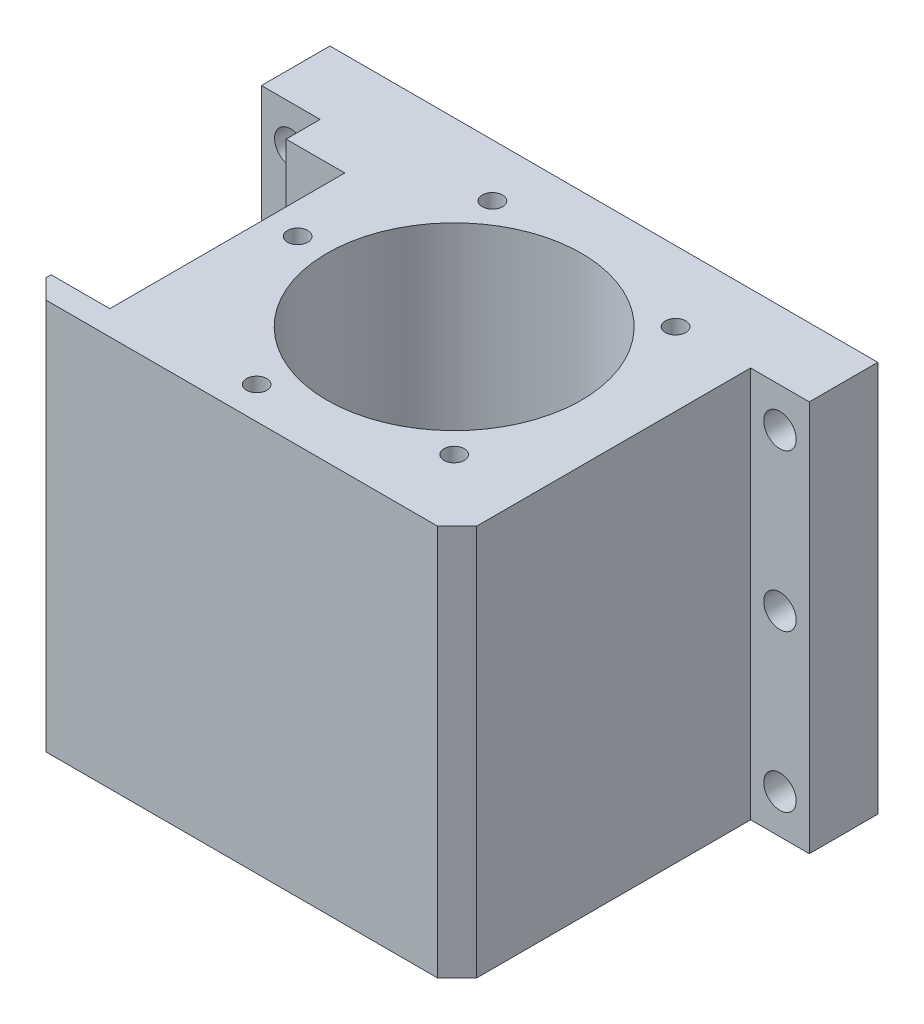
SolidWorks part; units mm, degrees
material "3.3315 (EN-AW 5005)"
ref_plane "前视基准面" through (0, 0, 0) normal (0, 0, 1) x (1, 0, 0)
ref_plane "上视基准面" through (0, 0, 0) normal (0, 1, 0) x (1, 0, 0)
ref_plane "右视基准面" through (0, 0, 0) normal (1, 0, 0) x (0, 0, -1)
other "Configuration Table"
sketch "草图1" plane through (0, 0, 0) normal (0, 0, 1) x (1, 0, 0)
  line L1 (0, 0) -> (140, 0)
  line L2 (0, 0) -> (0, -100)
  line L3 (0, -100) -> (140, -100)
  line L4 (140, 0) -> (140, -100)
  dimension "D1" = 140
  dimension "D2" = 100
extrude "凸台-拉伸1" add sketch "草图1" along normal blind 92.5
sketch "草图2" plane through (0, 0, 0) normal (0, 1, 0) x (1, 0, 0)
  line L0 (140, -46.25) -> (0, -46.25) construction
  line L1 (140, -92.5) -> (140, 0) construction
  line L2 (0, -92.5) -> (0, 0) construction
  circle A0 centre (78, -46.25) radius 32.525
  dimension "D1" = 65.05
  dimension "D2" = 62
extrude "切除-拉伸1" cut sketch "草图2" against normal through all
sketch "草图3" plane through (0, 0, 92.5) normal (0, 0, 1) x (1, 0, 0)
  line L0 (70, 0) -> (70, -100) construction
  line L1 (140, 0) -> (0, 0) construction
  line L2 (0, -100) -> (140, -100) construction
  line L3 (0, 0) -> (0, -100) construction
  line L4 (15, 0) -> (125, 0)
  line L5 (15, 0) -> (15, -100)
  line L6 (15, -100) -> (125, -100)
  line L7 (125, 0) -> (125, -100)
  dimension "D1" = 110
  dimension "D2" = 15
extrude "切除-拉伸2" cut sketch "草图3" against normal blind 75 flip side to cut
sketch "草图4" plane through (0, 0, 0) normal (0, 1, 0) x (1, 0, 0)
  circle A0 centre (78, -46.25) radius 46 construction
  dimension "D1" = 92
sketch "草图5" plane through (15, 0, 0) normal (-1, 0, 0) x (0, 0, 1)
  line L0 (46.25, 0) -> (46.25, -100) construction
  line L1 (92.25, 0) -> (0.25, 0) construction
  line L2 (17.5, -100) -> (92.5, -100) construction
  line L4 (26.2, 0) -> (86.25, 0)
  line L5 (26.2, 0) -> (26.2, -100)
  line L6 (26.2, -100) -> (86.25, -100)
  line L7 (86.25, 0) -> (86.25, -100)
  dimension "D1" = 60.05
  dimension "D2" = 40
extrude "切除-拉伸3" cut sketch "草图5" against normal blind 15
chamfer "倒角2" distance 5 angle 45 2 edges at (125, -50, 92.5) (15, -50, 92.5)
sketch "草图6" plane through (0, -100, 0) normal (0, -1, 0) x (1, 0, 0)
  line L0 (78, 46.25) -> (78, 92.25) construction
  circle A0 centre (78, 46.25) radius 39.5 construction
  circle A1 centre (78, 46.25) radius 46 construction
  circle A2 centre (78, 85.75) radius 2.6
  circle A3 centre (112.208, 66) radius 2.6
  circle A4 centre (112.208, 26.5) radius 2.6
  circle A5 centre (78, 6.75) radius 2.6
  circle A6 centre (43.792, 26.5) radius 2.6
  circle A7 centre (43.792, 66) radius 2.6
  point P20 (78, 46.25)
  dimension "D1" = 79
  dimension "D2" = 5.2
  dimension "D3" = 6
extrude "切除-拉伸4" cut sketch "草图6" against normal blind 20
sketch "草图9" plane through (0, 0, 17.5) normal (0, 0, 1) x (1, 0, 0)
  line L0 (0, 0) -> (0, -100) construction
  line L1 (15, 0) -> (0, 0) construction
  circle A0 centre (7.5, -10) radius 4.15
  circle A1 centre (132.5, -10) radius 4.15
  circle A2 centre (132.5, -50) radius 4.15
  circle A3 centre (132.5, -90) radius 4.15
  circle A4 centre (7.5, -50) radius 4.15
  circle A5 centre (7.5, -90) radius 4.15
  dimension "D1" = 8.3
  dimension "D4" = 2
  dimension "D2" = 7.5
  dimension "D3" = 10
  dimension "D5" = 3
extrude "切除-拉伸5" cut sketch "草图9" against normal through all
sketch "草图10" plane through (0, 0, 0) normal (0, 1, 0) x (1, 0, 0)
  line L0 (38, -46.25) -> (118, -46.25) construction
  line L1 (78, -46.25) -> (78, -6.25) construction
  line L2 (78, -46.25) -> (49.7157, -17.9657) construction
  circle A0 centre (78, -46.25) radius 40 construction
  circle A3 centre (106.2843, -17.9657) radius 2.6
  circle A4 centre (106.2843, -74.5343) radius 2.6
  circle A6 centre (38, -46.25) radius 2.6
  circle A7 centre (65.5345, -84.258) radius 2.6
  circle A8 centre (55.0258, -13.5057) radius 2.6
  point P18 (78, -46.25)
  dimension "D1" = 80
  dimension "D2" = 5.2
  dimension "D4" = 5.2
  dimension "D3" = 5.2
extrude "切除-拉伸6" cut sketch "草图10" against normal blind 20
